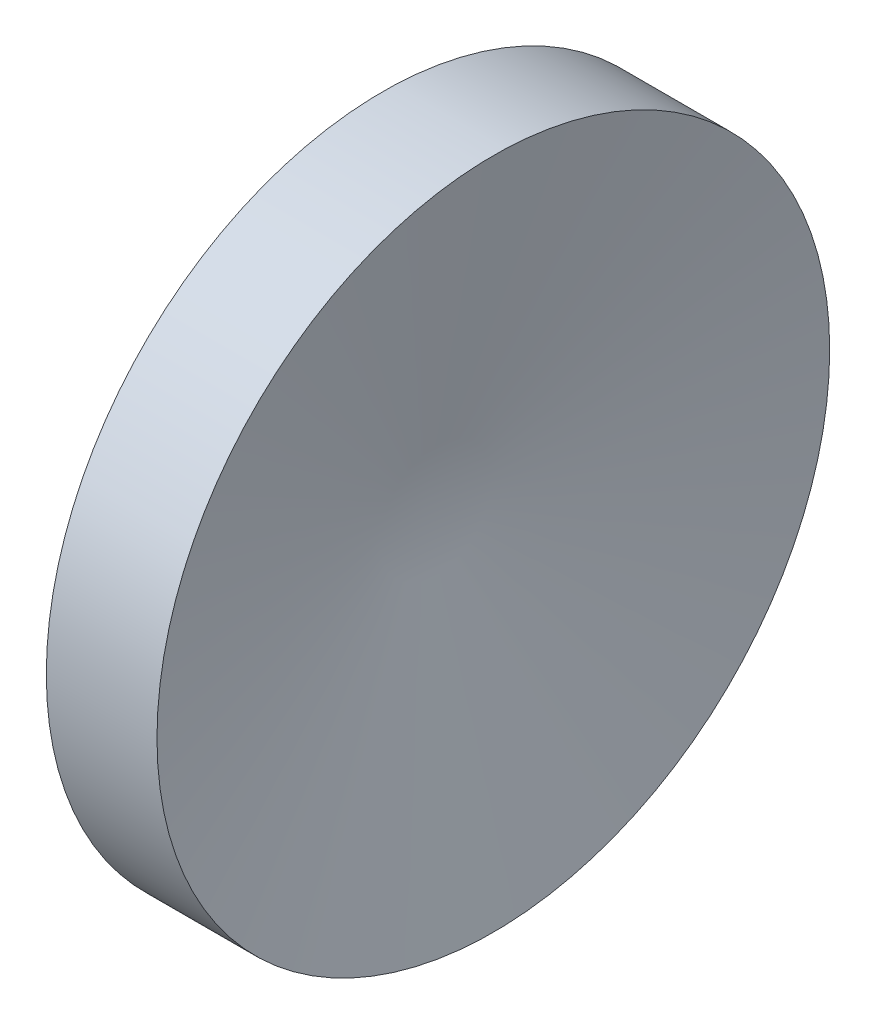
SolidWorks part; units mm, degrees
ref_plane "Alzado" through (0, 0, 0) normal (0, 0, 1) x (1, 0, 0)
ref_plane "Planta" through (0, 0, 0) normal (0, 1, 0) x (1, 0, 0)
ref_plane "Vista lateral" through (0, 0, 0) normal (1, 0, 0) x (0, 0, -1)
sketch "Croquis1" plane through (0, 0, 0) normal (0, 0, 1) x (1, 0, 0)
  line L0 (0, -30.5937) -> (0, 37.2348)
  line L1 (0, 37.2348) -> (22.3184, 37.2348)
  line L2 (22.3184, 37.2348) -> (8.4259, -30.5937)
  line L3 (8.4259, -30.5937) -> (0, -30.5937)
revolve "Revolución1" add sketch "Croquis1" angle 360 about L3
